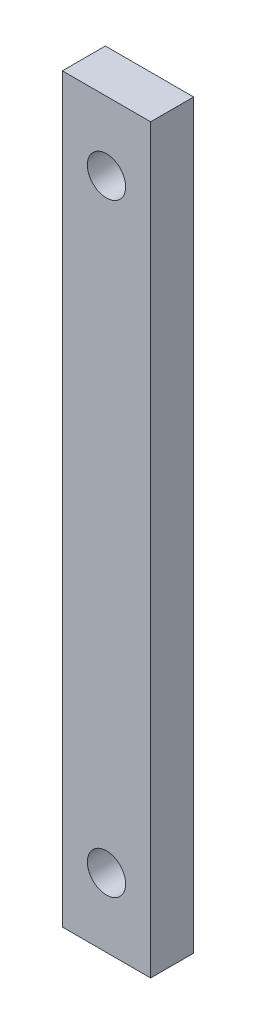
SolidWorks part; units mm, degrees
material "Maple"
ref_plane "Front Plane" through (0, 0, 0) normal (0, 0, 1) x (1, 0, 0)
ref_plane "Top Plane" through (0, 0, 0) normal (0, 1, 0) x (1, 0, 0)
ref_plane "Right Plane" through (0, 0, 0) normal (1, 0, 0) x (0, 0, -1)
sketch "Sketch1" plane through (0, 0, 0) normal (0, 0, 1) x (1, 0, 0)
  line L1 (-3.26, 27.385) -> (3.26, 27.385)
  line L2 (-3.26, 27.385) -> (-3.26, -27.385)
  line L3 (-3.26, -27.385) -> (3.26, -27.385)
  line L4 (3.26, 27.385) -> (3.26, -27.385)
  line L5 (-3.26, 27.385) -> (3.26, -27.385) construction
  line L6 (-3.26, -27.385) -> (3.26, 27.385) construction
  point P0 (0, 0)
  dimension "D1" = 6.52
  dimension "D2" = 54.77
extrude "Boss-Extrude1" add sketch "Sketch1" along normal blind 3.175
sketch "Sketch2" plane through (0, 0, 3.175) normal (0, 0, 1) x (1, 0, 0)
  line L0 (0, 27.385) -> (0, -27.385) construction
  line L1 (3.26, 27.385) -> (-3.26, 27.385) construction
  line L2 (-3.26, -27.385) -> (3.26, -27.385) construction
  line L3 (0, 0) -> (-2.9257, 0) construction
  line L4 (-3.26, 27.385) -> (-3.26, -27.385) construction
  circle A0 centre (0, 22.295) radius 1.415
  circle A1 centre (0, -22.295) radius 1.415
  point P6 (0, 22.295)
  dimension "D2" = 2.83
  dimension "D1" = 5.09
extrude "Cut-Extrude1" cut sketch "Sketch2" against normal through all
equation "\"kerf\"= 0.17 / 2"
equation "\"D1@Sketch1\"= 6.35mm + 2*\"kerf\""
equation "\"D2@Sketch1\"= 54.60mm + 2*\"kerf\""
